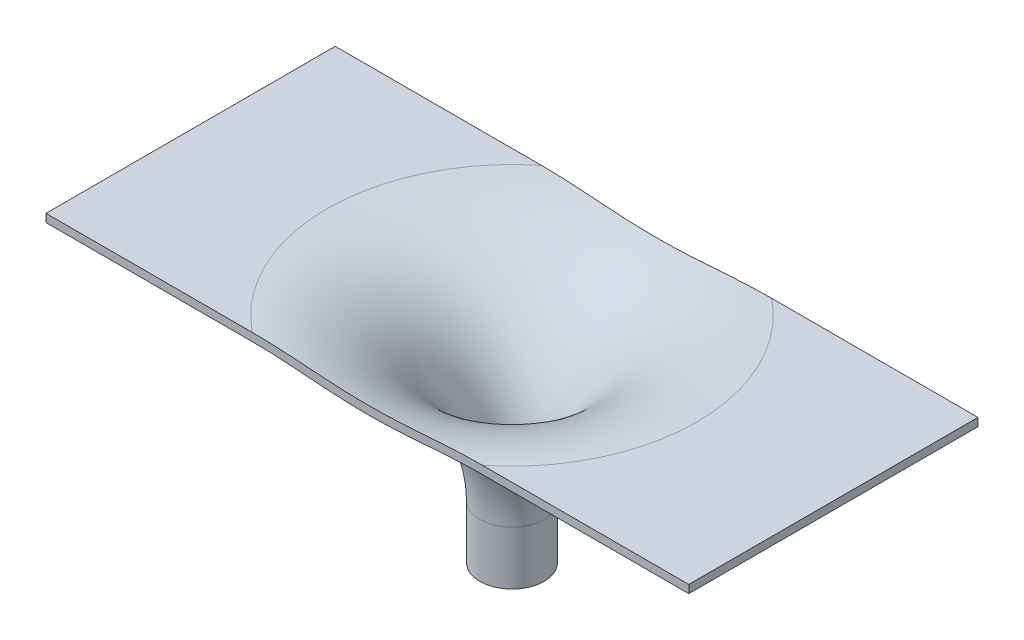
SolidWorks part; units mm, degrees
ref_plane "Plan de face" through (0, 0, 0) normal (0, 0, 1) x (1, 0, 0)
ref_plane "Plan de dessus" through (0, 0, 0) normal (0, 1, 0) x (1, 0, 0)
ref_plane "Plan de droite" through (0, 0, 0) normal (1, 0, 0) x (0, 0, -1)
sketch "Esquisse1" plane through (0, 0, 0) normal (1, 0, 0) x (0, 0, -1)
  line L2 (13.2296, -67.5152) -> (13.2296, 136.6424) construction
  line L5 (-1.7704, -67.5152) -> (-1.7704, -34.1115)
  line L7 (-101.7704, 65.8885) -> (-186.7704, 65.8885)
  line L8 (-186.7704, 65.8885) -> (-186.7704, 60.8885)
  line L9 (-1.7704, -67.5152) -> (-6.7704, -67.5152)
  line L10 (-6.7704, -67.5152) -> (-6.7704, -34.1115)
  line L11 (-186.7704, 60.8885) -> (-101.7704, 60.8885)
  arc A0 (-1.7704, -34.1115) -> (-101.7704, 65.8885) centre (-101.7704, -34.1115) ccw
  arc A1 (-101.7704, 60.8885) -> (-6.7704, -34.1115) centre (-101.7704, -34.1115) cw
  dimension "D1" = 100
  dimension "D3" = 15
  dimension "D6" = 85
  dimension "D7" = 5
  dimension "D8" = 5
revolve "Révolution3" add sketch "Esquisse1" angle 360 about L2
ref_plane "Plan2" through (0, 65.8885, 0) normal (0, 1, 0) x (1, 0, 0)
sketch "Esquisse4" plane through (0, 65.8885, 0) normal (0, 1, 0) x (1, 0, 0)
  line L0 (200, -76.7704) -> (200, -208.3486)
  line L3 (-200, 103.2296) -> (200, 103.2296)
  line L5 (200, -76.7704) -> (-200, -76.7704)
  line L6 (200, -208.3486) -> (-200, -208.3486)
  line L7 (-200, -208.3486) -> (-200, -76.7704)
  line L8 (-200, 103.2296) -> (-200, 233.0488)
  line L9 (-200, 233.0488) -> (200, 233.0488)
  line L10 (200, 233.0488) -> (200, 103.2296)
extrude "Enlèv. mat.-Extru.1" cut sketch "Esquisse4" against normal blind 10
sketch "Esquisse5" plane through (0, 65.8885, 0) normal (0, 1, 0) x (1, 0, 0)
  line L0 (-200, 13.2296) -> (-200, 103.2296)
  line L1 (-200, 103.2296) -> (-178.6057, 103.2296)
  line L2 (-200, 13.2296) -> (-200, -76.7704)
  line L3 (-200, -76.7704) -> (-178.6057, -76.7704)
  line L4 (200, 13.2296) -> (200, 103.2296)
  line L5 (200, 103.2296) -> (178.6057, 103.2296)
  line L6 (200, 13.2296) -> (200, -76.7704)
  line L7 (200, -76.7704) -> (178.6057, -76.7704)
  line L8 (-178.6057, 103.2296) -> (-178.6057, -76.7704)
  line L9 (178.6057, 103.2296) -> (178.6057, -76.7704)
  line L10 (-200, 13.2296) -> (200, 13.2296) construction
  arc A0 (-178.6057, 103.2296) -> (-178.6057, -76.7704) centre (0, 13.2296) ccw construction
  arc A1 (178.6057, -76.7704) -> (178.6057, 103.2296) centre (0, 13.2296) ccw construction
extrude "Boss.-Extru.2" add sketch "Esquisse5" against normal blind 5
